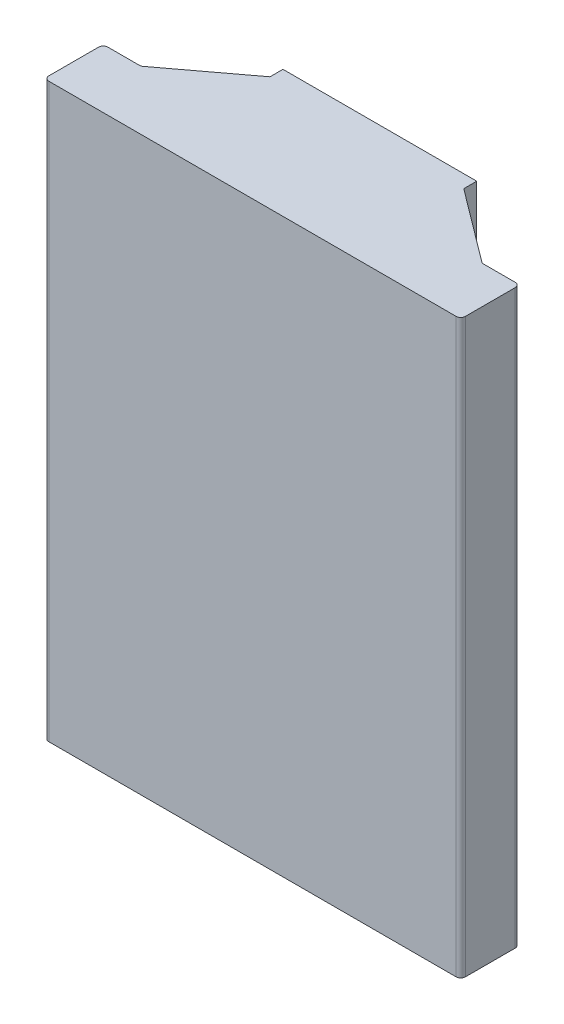
SolidWorks part; units mm, degrees
ref_plane "Front Plane" through (0, 0, 0) normal (0, 0, 1) x (1, 0, 0)
ref_plane "Top Plane" through (0, 0, 0) normal (0, 1, 0) x (1, 0, 0)
ref_plane "Right Plane" through (0, 0, 0) normal (1, 0, 0) x (0, 0, -1)
sketch "Sketch2" plane through (0, 0, 0) normal (0, 1, 0) x (1, 0, 0)
  line L0 (-20.575, 0) -> (20.575, 0)
  line L1 (-20.575, 0) -> (-20.575, 2.4)
  line L2 (20.575, 0) -> (20.575, 2.4)
  line L3 (-20.575, 2.4) -> (-17.825, 2.4)
  line L4 (20.575, 2.4) -> (17.825, 2.4)
  line L5 (-8.5, 9.4) -> (8.5, 9.4) construction
  line L6 (-17.825, 2.4) -> (-8.5, 9.4)
  line L7 (17.825, 2.4) -> (8.5, 9.4)
  line L9 (-10.5, 10.3995) -> (-18.4921, 4.4)
  line L10 (-18.4921, 4.4) -> (-22.575, 4.4)
  line L11 (-22.575, 4.4) -> (-22.575, -2)
  line L12 (-22.575, -2) -> (22.575, -2)
  line L13 (22.575, -2) -> (22.575, 4.4)
  line L14 (22.575, 4.4) -> (18.4921, 4.4)
  line L15 (18.4921, 4.4) -> (10.5, 10.3995)
  line L17 (-10.5, 10.3995) -> (-10.5, 11.805)
  line L18 (-10.5, 11.805) -> (-8.5, 11.805)
  line L19 (-8.5, 11.805) -> (-8.5, 9.4)
  line L20 (8.5, 9.4) -> (8.5, 11.805)
  line L21 (8.5, 11.805) -> (10.5, 11.805)
  line L22 (10.5, 11.805) -> (10.5, 10.3995)
  point P3 (0, 0)
  point P11 (0, 9.4)
  dimension "D1" = 41.15
  dimension "D2" = 2.4
  dimension "D3" = 2.4
  dimension "D4" = 2.75
  dimension "D5" = 2.75
  dimension "D6" = 17
  dimension "D7" = 7
  dimension "D8" = 2
  dimension "D9" = 2
  dimension "D10" = 2
  dimension "D11" = 2
  dimension "D12" = 2
  dimension "D13" = 2
  dimension "D14" = 2
  dimension "D15" = 2
  dimension "D16" = 2
extrude "Boss-Extrude1" add sketch "Sketch2" along normal blind 60
sketch "Sketch4" plane through (0, 60, 0) normal (0, 1, 0) x (1, 0, 0)
  line L0 (-22.575, 4.4) -> (-22.575, -2)
  line L1 (-22.575, 4.4) -> (-22.575, -2) construction
  line L2 (-22.575, -2) -> (22.575, -2)
  line L3 (22.575, -2) -> (22.575, 4.4)
  line L4 (22.575, 4.4) -> (18.4921, 4.4) construction
  line L5 (22.575, -2) -> (22.575, 4.4) construction
  line L6 (22.575, 4.4) -> (18.4921, 4.4)
  line L7 (18.4921, 4.4) -> (10.5, 10.3995)
  line L8 (10.5, 10.3995) -> (10.5, 11.805)
  line L9 (10.5, 11.805) -> (8.5, 11.805) construction
  line L10 (10.5, 10.3995) -> (10.5, 11.805) construction
  line L11 (10.5, 11.805) -> (-10.5, 11.805)
  line L12 (-10.5, 11.805) -> (-10.5, 10.3995)
  line L13 (-10.5, 10.3995) -> (-18.4921, 4.4)
  line L14 (-18.4921, 4.4) -> (-22.575, 4.4)
extrude "Boss-Extrude2" add sketch "Sketch4" along normal blind 2
fillet "Fillet1" radius 0.5 12 edges at (8.5, 30, -9.4) (-8.5, 30, -9.4) (-18.4921, 31, -4.4) (18.4921, 31, -4.4) (22.575, 31, -4.4) (22.575, 31, 2) (-22.575, 31, -4.4) (-22.575, 31, 2) (20.575, 30, -2.4) (20.575, 30, 0) (-20.575, 30, 0) (-20.575, 30, -2.4)
equation "\"D3@Sketch2\"=\"D2@Sketch2\""
equation "\"D5@Sketch2\"=\"D4@Sketch2\""
